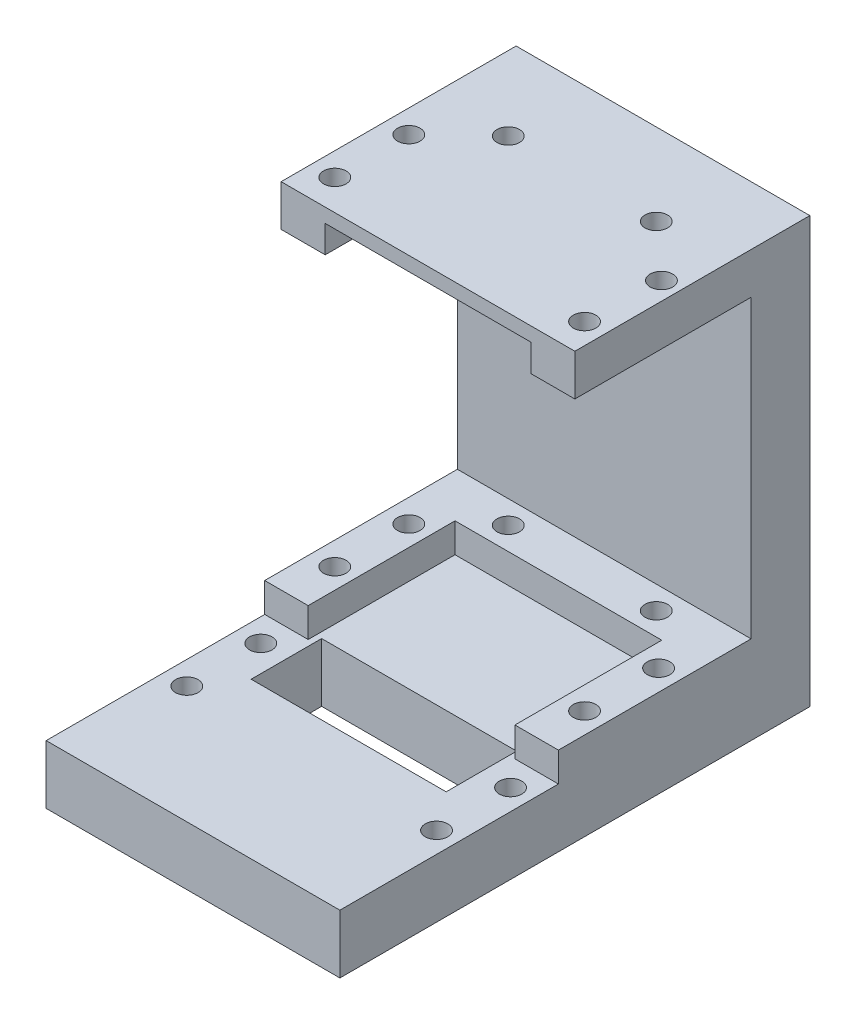
SolidWorks part; units mm, degrees
ref_plane "Front Plane" through (0, 0, 0) normal (0, 0, 1) x (1, 0, 0)
ref_plane "Top Plane" through (0, 0, 0) normal (0, 1, 0) x (1, 0, 0)
ref_plane "Right Plane" through (0, 0, 0) normal (1, 0, 0) x (0, 0, -1)
sketch "Sketch1" plane through (0, 0, 0) normal (0, 1, 0) x (1, 0, 0)
  line L1 (-15.875, 25.4) -> (15.875, 25.4)
  line L2 (-15.875, 25.4) -> (-15.875, -25.4)
  line L3 (-15.875, -25.4) -> (15.875, -25.4)
  line L4 (15.875, 25.4) -> (15.875, -25.4)
  line L5 (-15.875, 25.4) -> (15.875, -25.4) construction
  line L6 (-15.875, -25.4) -> (15.875, 25.4) construction
  point P0 (0, 0)
  dimension "D1" = 50.8
  dimension "D2" = 31.75
extrude "Boss-Extrude1" add sketch "Sketch1" along normal blind 45.974
sketch "Sketch2" plane through (-15.875, 0, 0) normal (-1, 0, 0) x (0, 0, 1)
  line L0 (-25.4, 45.974) -> (-25.4, 0) construction
  line L1 (25.4, 0) -> (1.778, 0)
  line L2 (25.4, 0) -> (25.4, 6.35)
  line L3 (25.4, 6.35) -> (1.778, 6.35)
  line L5 (25.4, 0) -> (1.778, 6.35) construction
  line L6 (25.4, 6.35) -> (1.778, 0) construction
  line L7 (1.778, 0) -> (-25.4, 0)
  line L8 (1.778, 6.35) -> (1.778, 9.525)
  line L9 (1.778, 9.525) -> (-19.05, 9.525)
  line L10 (-25.4, 0) -> (-25.4, 9.525)
  line L11 (1.778, 0) -> (-25.4, 9.525) construction
  line L12 (1.778, 9.525) -> (-25.4, 0) construction
  line L13 (-25.4, 45.974) -> (25.4, 45.974) construction
  line L15 (-25.4, 9.525) -> (-25.4, 45.974)
  line L16 (-25.4, 45.974) -> (-19.05, 45.974)
  line L17 (-19.05, 9.525) -> (-19.05, 41.5036)
  line L18 (-25.4, 9.525) -> (-19.05, 45.974) construction
  line L19 (-25.4, 45.974) -> (-19.05, 9.525) construction
  line L20 (25.4, 45.974) -> (25.4, 0) construction
  line L21 (-19.05, 45.974) -> (25.4, 45.974)
  line L23 (-19.05, 41.5036) -> (25.4, 41.5036)
  line L24 (25.4, 45.974) -> (25.4, 41.5036)
  line L25 (-19.05, 45.974) -> (25.4, 41.5036) construction
  line L26 (-19.05, 41.5036) -> (25.4, 45.974) construction
  line L27 (25.4, 41.5036) -> (25.4, 6.35)
  point P4 (13.589, 3.175)
  point P9 (-11.811, 4.7625)
  point P15 (-22.225, 27.7495)
  point P21 (3.175, 43.7388)
  line M13 (25.4, 0) -> (25.4, 45.974)
  dimension "D1" = 23.622
  dimension "D2" = 6.35
  dimension "D3" = 3.175
  dimension "D4" = 27.178
  dimension "D5" = 6.35
  dimension "D6" = 4.4704
extrude "Cut-Extrude1" cut sketch "Sketch2" against normal through all contours L23 L17 L9 L8 L3 M13
sketch "Sketch3" plane through (0, 9.525, 0) normal (0, 1, 0) x (1, 0, 0)
  line L0 (15.875, -1.778) -> (-15.875, -1.778) construction
  line L1 (-11.176, -1.778) -> (11.176, -1.778)
  line L2 (-11.176, -1.778) -> (-11.176, 14.097)
  line L3 (-11.176, 14.097) -> (11.176, 14.097)
  line L4 (11.176, -1.778) -> (11.176, 14.097)
  line L5 (-11.176, -1.778) -> (11.176, 14.097) construction
  line L6 (-11.176, 14.097) -> (11.176, -1.778) construction
  line L7 (15.875, 19.05) -> (-15.875, 19.05) construction
  point P4 (0, 6.1595)
  point P7 (0, 0)
  point P8 (-7.6601, 6.1595)
  point P11 (0, 19.05)
  dimension "D1" = 15.875
  dimension "D2" = 22.352
extrude "Cut-Extrude2" cut sketch "Sketch3" against normal up to surface (3.175 mm away) up to face at (0, 6.35, 13.589)
sketch "Sketch4" plane through (0, 45.974, 0) normal (0, 1, 0) x (1, 0, 0)
  line L0 (15.875, -25.4) -> (15.875, 25.4) construction
  line L1 (-15.875, -25.4) -> (15.875, -25.4)
  line L2 (-15.875, -25.4) -> (-15.875, 0)
  line L3 (-15.875, 0) -> (15.875, 0)
  line L4 (15.875, -25.4) -> (15.875, 0)
  line L5 (-15.875, -25.4) -> (15.875, 0) construction
  line L6 (-15.875, 0) -> (15.875, -25.4) construction
  point P4 (0, -12.7)
  dimension "D1" = 25.4
extrude "Cut-Extrude3" cut sketch "Sketch4" against normal up to surface (4.4704 mm away) up to face at (0, 41.5036, 3.175)
sketch "Sketch5" plane through (0, 45.974, 0) normal (0, 1, 0) x (1, 0, 0)
  line L0 (15.875, 0) -> (-15.875, 0) construction
  line L1 (-11.1125, 0) -> (11.1125, 0)
  line L2 (-11.1125, 0) -> (-11.1125, 12.7)
  line L3 (-11.1125, 12.7) -> (11.1125, 12.7)
  line L4 (11.1125, 0) -> (11.1125, 12.7)
  line L5 (-11.1125, 0) -> (11.1125, 12.7) construction
  line L6 (-11.1125, 12.7) -> (11.1125, 0) construction
  line L7 (15.875, 25.4) -> (-15.875, 25.4) construction
  point P4 (0, 6.35)
  point P7 (0, 0)
  point P10 (0, 25.4)
  dimension "D1" = 22.225
  dimension "D2" = 12.7
extrude "Cut-Extrude4" cut sketch "Sketch5" against normal up to surface (2.9464 mm away) from offset 1.524 up to face at (0, 41.5036, -9.525) offset against normal yes
hole_wizard "#2 Clearance Hole1" positions "Sketch6" profile "Sketch7" hole size "#2" standard "ANSI Inch"
sketch "Sketch6" plane through (0, 9.525, 0) normal (0, 1, 0) x (1, 0, 0)
  point P0 (-13.375, 11.3)
  point P3 (-13.375, 3.3)
  point P6 (-7.875, 16.55)
  point P9 (8.125, 16.55)
  point P14 (13.625, 3.3)
  point P19 (13.625, 11.3)
sketch "Sketch7" plane through (-13.375, 9.525, -11.3) normal (1, 0, 0) x (0, 0, 1)
  line L0 (0, 0) -> (0, 9.525)
  line L1 (0, 9.525) -> (1.2192, 9.525)
  line L2 (1.2192, 9.525) -> (1.2192, 0)
  line L5 (1.2192, 0) -> (0, 0)
  line L11 (0, -6.35) -> (0, 107.95) construction
  dimension "Thru Hole Dia." = 2.4384
  dimension "Thru Hole Depth" = 9.525
hole_wizard "#2 Clearance Hole2" positions "Sketch8" profile "Sketch9" hole size "#2" standard "ANSI Inch"
sketch "Sketch8" plane through (0, 41.5036, 0) normal (0, -1, 0) x (-1, 0, 0)
  point P0 (13.375, 11.3)
  point P5 (7.875, 16.55)
  point P8 (-8.125, 16.55)
  point P11 (-13.9328, 11.3)
  point P13 (-13.625, 3.3)
  point P17 (13.375, 3.3)
sketch "Sketch9" plane through (-13.375, 41.5036, -11.3) normal (1, 0, 0) x (0, 0, -1)
  line L0 (0, 0) -> (0, 4.4704)
  line L1 (0, 4.4704) -> (1.2192, 4.4704)
  line L2 (1.2192, 4.4704) -> (1.2192, 0)
  line L5 (1.2192, 0) -> (0, 0)
  line L11 (0, -6.35) -> (0, 107.95) construction
  dimension "Thru Hole Dia." = 2.4384
  dimension "Thru Hole Depth" = 4.4704
sketch "Sketch10" plane through (0, 6.35, 0) normal (0, 1, 0) x (1, 0, 0)
  line L0 (15.875, 0) -> (-15.875, 0) construction
  line L1 (-10.541, -0.9578) -> (10.541, -0.9578)
  line L2 (-10.541, -0.9578) -> (-10.541, -8.5778)
  line L3 (-10.541, -8.5778) -> (10.541, -8.5778)
  line L4 (10.541, -0.9578) -> (10.541, -8.5778)
  line L5 (-10.541, -0.9578) -> (10.541, -8.5778) construction
  line L6 (-10.541, -8.5778) -> (10.541, -0.9578) construction
  line L7 (15.875, -25.4) -> (-15.875, -25.4) construction
  point P4 (0, -4.7678)
  point P5 (0, 0)
  point P8 (0, 0)
  dimension "D1" = 21.082
  dimension "D2" = 7.62
  dimension "D3" = 20.6322
extrude "Cut-Extrude5" cut sketch "Sketch10" against normal up to surface (6.35 mm away) up to face at (-13.375, 0, -10.0808)
hole_wizard "#2 Clearance Hole3" positions "Sketch11" profile "Sketch12" hole size "#2" standard "ANSI Inch" end condition through all
sketch "Sketch11" plane through (0, 6.35, 0) normal (0, 1, 0) x (1, 0, 0)
  point P0 (-13.375, -4.7)
  point P3 (-13.375, -12.7)
  point P6 (13.625, -12.7)
  point P9 (13.625, -4.7)
sketch "Sketch12" plane through (-13.375, 6.35, 4.7) normal (1, 0, 0) x (0, 0, 1)
  line L0 (0, 0) -> (0, 6.35)
  line L1 (0, 6.35) -> (1.2192, 6.35)
  line L2 (1.2192, 6.35) -> (1.2192, 0)
  line L5 (1.2192, 0) -> (0, 0)
  line L11 (0, -6.35) -> (0, 107.95) construction
  dimension "Thru Hole Dia." = 2.4384
  dimension "Thru Hole Depth" = 6.35
